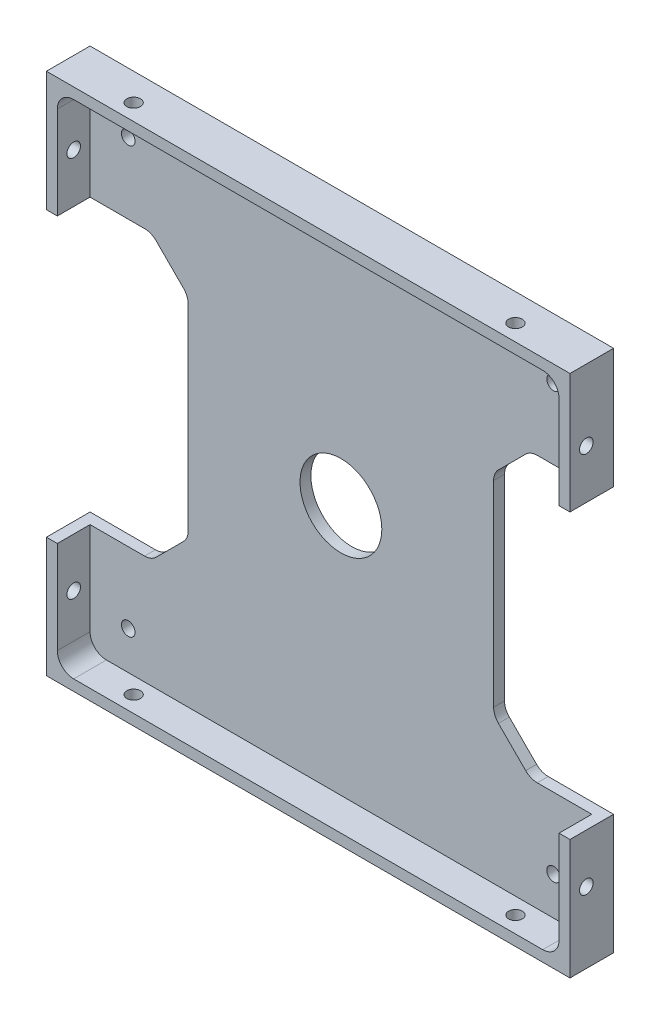
SolidWorks part; units mm, degrees
material "6061-T6 (SS)"
ref_plane "Front" through (0, 0, 0) normal (0, 0, 1) x (1, 0, 0)
ref_plane "Top" through (0, 0, 0) normal (0, 1, 0) x (1, 0, 0)
ref_plane "Right" through (0, 0, 0) normal (1, 0, 0) x (0, 0, -1)
sketch "Sketch1" plane through (0, 0, 0) normal (0, 0, 1) x (1, 0, 0)
  line L1 (-48, -48) -> (48, -48)
  line L2 (-48, -48) -> (-48, 48)
  line L3 (-48, 48) -> (48, 48)
  line L4 (48, -48) -> (48, 48)
  line L5 (-48, -48) -> (48, 48) construction
  line L6 (-48, 48) -> (48, -48) construction
  point P0 (0, 0)
  dimension "D1" = 96
  dimension "D2" = 96
extrude "Boss-Extrude1" add sketch "Sketch1" along normal blind 8
sketch "Sketch2" plane through (0, 0, 8) normal (0, 0, 1) x (1, 0, 0)
  line L1 (46, -46) -> (-46, -46)
  line L2 (46, -46) -> (46, 46)
  line L3 (46, 46) -> (-46, 46)
  line L4 (-46, -46) -> (-46, 46)
  line L5 (46, -46) -> (-46, 46) construction
  line L6 (46, 46) -> (-46, -46) construction
  point P0 (0, 0)
  dimension "D1" = 92
  dimension "D2" = 92
extrude "Component Platform" cut sketch "Sketch2" against normal blind 6
sketch "Sketch3" plane through (0, 0, 2) normal (0, 0, 1) x (1, 0, 0)
  line L1 (-33.8787, -25.1213) -> (-28.8787, -20.1213)
  line L2 (-33.8787, 25.1213) -> (-28.8787, 20.1213)
  line L3 (-28, -18) -> (-28, 18)
  line L4 (-48, -26) -> (-36, -26)
  line L7 (-48, 48) -> (-48, -48) construction
  line L8 (0, -56.7987) -> (0, 73.4321) construction
  line L9 (46, -46) -> (-57.8147, 57.8147) construction
  line L18 (46, 46) -> (-68.5705, -68.5705) construction
  line L23 (-48, 26) -> (-36, 26)
  line L26 (-48, -26) -> (-48, 26)
  line L28 (-48, -48) -> (48, -48) construction
  line L29 (48, -26) -> (48, 26)
  line L30 (48, 26) -> (36, 26)
  line L31 (33.8787, 25.1213) -> (28.8787, 20.1213)
  line L32 (28, -18) -> (28, 18)
  line L33 (33.8787, -25.1213) -> (28.8787, -20.1213)
  line L34 (48, -26) -> (36, -26)
  arc A3 (-28.8787, -20.1213) -> (-28, -18) centre (-31, -18) ccw
  arc A4 (-28.8787, 20.1213) -> (-28, 18) centre (-31, 18) cw
  arc A13 (-33.8787, -25.1213) -> (-36, -26) centre (-36, -23) cw
  arc A15 (-33.8787, 25.1213) -> (-36, 26) centre (-36, 23) ccw
  arc A17 (33.8787, 25.1213) -> (36, 26) centre (36, 23) cw
  arc A18 (28.8787, 20.1213) -> (28, 18) centre (31, 18) ccw
  arc A19 (28.8787, -20.1213) -> (28, -18) centre (31, -18) cw
  arc A20 (33.8787, -25.1213) -> (36, -26) centre (36, -23) ccw
  point P0 (-48, 0)
  point P37 (-48, 0)
  dimension "D2" = 3
  dimension "D3" = 3
  dimension "D4" = 20
  dimension "D6" = 3
  dimension "D7" = 3
  dimension "D8" = 135
  dimension "D5" = 52
  dimension "D9" = 135
  dimension "D10" = 12
  dimension "D11" = 12
  dimension "D12" = 48
extrude "Cable Slots" cut sketch "Sketch3" against normal mid plane 12
sketch "Sketch4" plane through (0, 0, 2) normal (0, 0, 1) x (1, 0, 0)
  circle A0 centre (0, 0) radius 7.5
  dimension "D1" = 15
extrude "Center Mass Cut" cut sketch "Sketch4" against normal blind 6
ref_plane "Center Y-Plane" through (0, 0, 0) normal (1, 0, 0) x (0, 0, -1)
ref_plane "Center X-Plane" through (0, 0, 0) normal (0, -1, 0) x (-1, 0, 0)
fillet "Inner Corner Fillets" radius 3 4 edges at (46, -46, 5) (-46, -46, 5) (46, 46, 5) (-46, 46, 5)
sketch "Sketch7" plane through (0, 0, 2) normal (0, 0, 1) x (1, 0, 0)
  line L1 (39, -39) -> (-39, -39)
  line L2 (39, -39) -> (39, 39)
  line L3 (39, 39) -> (-39, 39)
  line L4 (-39, -39) -> (-39, 39)
  line L5 (39, -39) -> (-39, 39) construction
  line L6 (39, 39) -> (-39, -39) construction
  point P0 (0, 0)
  dimension "D1" = 78
  dimension "D2" = 78
sketch "Sketch8" plane through (0, -48, 0) normal (0, -1, 0) x (-1, 0, 0)
  line L0 (48, -5) -> (-48, -5) construction
  line L1 (48, -8) -> (48, 0) construction
  line L2 (-48, -8) -> (-48, 0) construction
  line L3 (48, -8) -> (-48, -8) construction
  dimension "D1" = 3
sketch "Sketch9" plane through (48, 0, 0) normal (1, 0, 0) x (0, 0, -1)
  line L0 (-5, 48) -> (-5, -48) construction
  line L1 (-8, 48) -> (0, 48) construction
  line L2 (-8, -48) -> (0, -48) construction
  line L3 (-8, 26) -> (-8, 48) construction
  dimension "D1" = 3
hole_wizard "M3x0.5 Tapped Hole1" positions "Sketch10" profile "Sketch11" tap size "M3x0.5" standard "ANSI Metric"
sketch "Sketch10" plane through (0, -48, 0) normal (0, -1, 0) x (-1, 0, 0)
  line L0 (48, -5) -> (-48, -5) construction
  point P0 (35, -5)
  point P4 (-35, -5)
  dimension "D1" = 70
  dimension "D2" = 35
sketch "Sketch11" plane through (-35, -48, 5) normal (1, 0, 0) x (0, 0, -1)
  line L0 (0, 0) -> (0, 10.7511)
  line L1 (0, 10.7511) -> (1.25, 10)
  line L2 (1.25, 10) -> (1.25, 0)
  line L5 (1.25, 0) -> (0, 0)
  line L10 (0, 10.7511) -> (-1.25, 10) construction
  line L11 (0, -6.35) -> (0, 107.95) construction
  dimension "Tap Drill Dia." = 2.5
  dimension "Tap Drill Depth" = 10
  dimension "Drill Angle" = 118
hole_wizard "M3x0.5 Tapped Hole2" positions "Sketch12" profile "Sketch13" tap size "M3x0.5" standard "ANSI Metric"
sketch "Sketch12" plane through (48, 0, 0) normal (1, 0, 0) x (0, 0, -1)
  line L0 (-5, 48) -> (-5, -48) construction
  point P0 (-5, -35)
  point P4 (-5, 35)
  dimension "D1" = 70
  dimension "D2" = 35
sketch "Sketch13" plane through (48, -35, 5) normal (0, 1, 0) x (0, 0, -1)
  line L0 (0, 0) -> (0, 10.7511)
  line L1 (0, 10.7511) -> (1.25, 10)
  line L2 (1.25, 10) -> (1.25, 0)
  line L5 (1.25, 0) -> (0, 0)
  line L10 (0, 10.7511) -> (-1.25, 10) construction
  line L11 (0, -6.35) -> (0, 107.95) construction
  dimension "Tap Drill Dia." = 2.5
  dimension "Tap Drill Depth" = 10
  dimension "Drill Angle" = 118
mirror "Mirror1" about plane through (0, 0, 0) normal (0, -1, 0) of "M3x0.5 Tapped Hole1"
mirror "Mirror2" about plane through (0, 0, 0) normal (1, 0, 0) of "M3x0.5 Tapped Hole2"
hole_wizard "M3x0.5 Tapped Hole3" positions "Sketch14" profile "Sketch15" tap size "M3x0.5" standard "ANSI Metric"
sketch "Sketch14" plane through (0, 0, 2) normal (0, 0, 1) x (1, 0, 0)
  point P0 (-39, -39)
  point P3 (39, -39)
  point P6 (39, 39)
  point P9 (-39, 39)
sketch "Sketch15" plane through (-39, -39, 2) normal (1, 0, 0) x (0, -1, 0)
  line L0 (0, 0) -> (0, 10.7511)
  line L1 (0, 10.7511) -> (1.25, 10)
  line L2 (1.25, 10) -> (1.25, 0)
  line L5 (1.25, 0) -> (0, 0)
  line L10 (0, 10.7511) -> (-1.25, 10) construction
  line L11 (0, -6.35) -> (0, 107.95) construction
  dimension "Tap Drill Dia." = 2.5
  dimension "Tap Drill Depth" = 10
  dimension "Drill Angle" = 118
